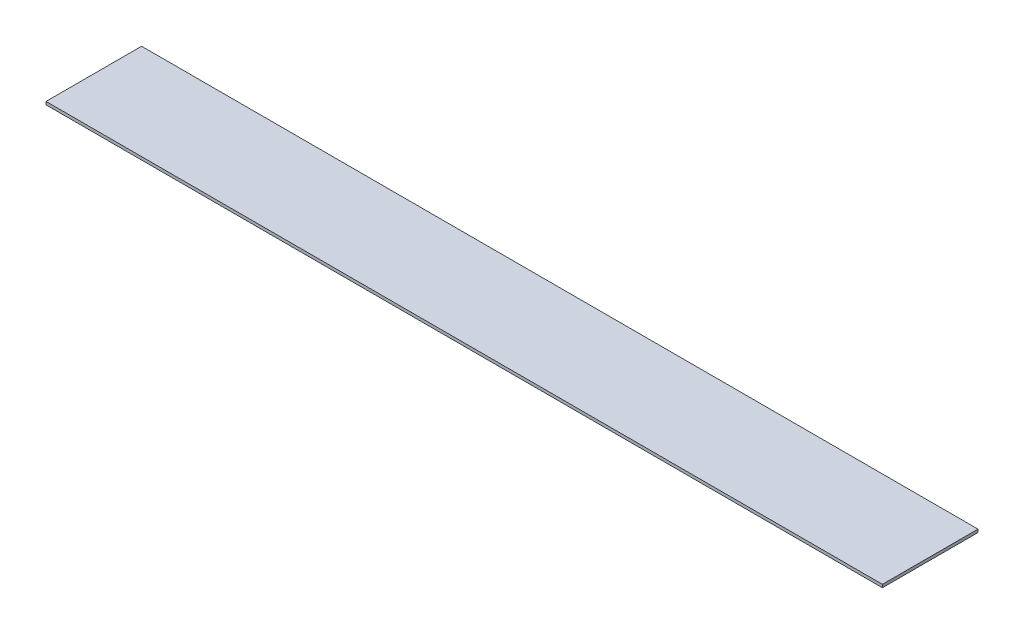
SolidWorks part; units mm, degrees
ref_plane "Front Plane" through (0, 0, 0) normal (0, 0, 1) x (1, 0, 0)
ref_plane "Top Plane" through (0, 0, 0) normal (0, 1, 0) x (1, 0, 0)
ref_plane "Right Plane" through (0, 0, 0) normal (1, 0, 0) x (0, 0, -1)
sketch "Sketch1" plane through (0, 0, 0) normal (0, 1, 0) x (1, 0, 0)
  line L1 (0, 0) -> (444.5, 0)
  line L2 (0, 0) -> (0, 50.8)
  line L3 (0, 50.8) -> (444.5, 50.8)
  line L4 (444.5, 0) -> (444.5, 50.8)
  dimension "D1" = 444.5
  dimension "D2" = 50.8
extrude "Boss-Extrude1" add sketch "Sketch1" along normal blind 1.5875
